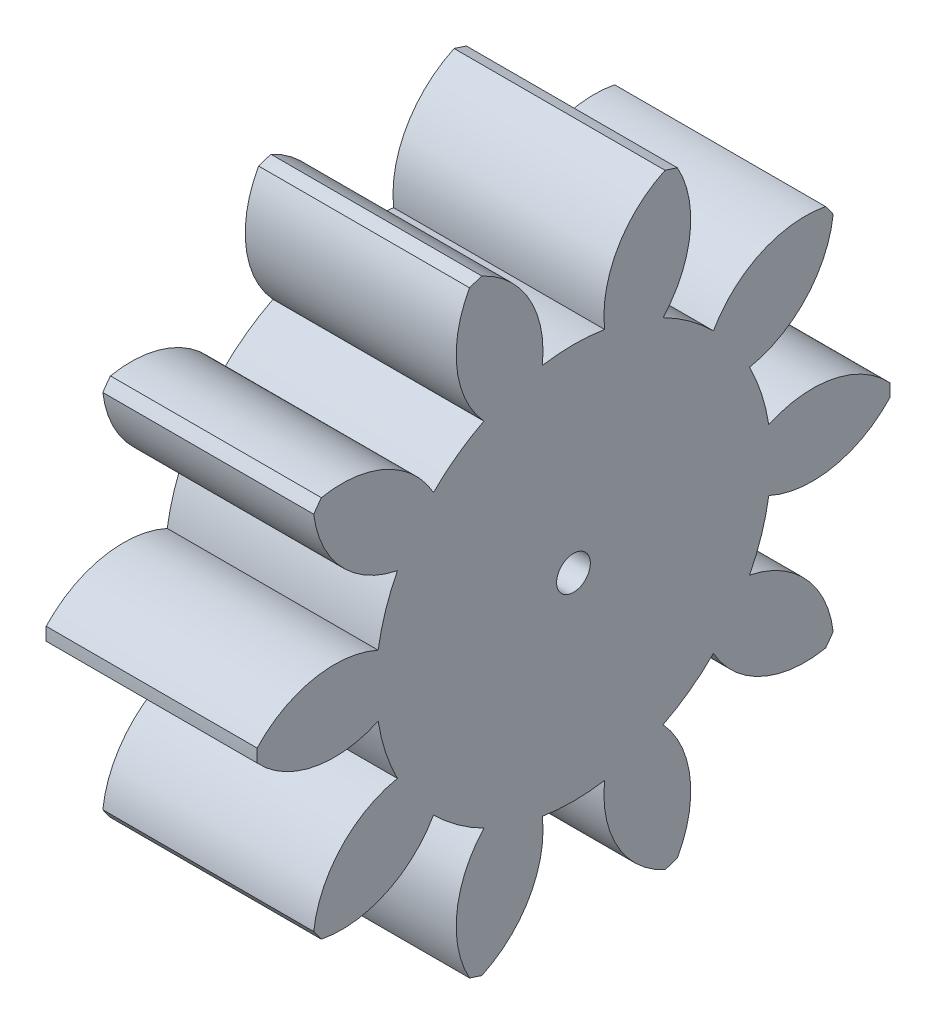
SolidWorks part; units mm, degrees
ref_plane "Plane1" through (0, 0, 0) normal (0, 0, 1) x (1, 0, 0)
ref_plane "Plane2" through (0, 0, 0) normal (0, 1, 0) x (1, 0, 0)
ref_plane "Plane3" through (0, 0, 0) normal (1, 0, 0) x (0, 0, -1)
sketch "HoldingSke" plane through (0, 0, 0) normal (0, 1, 0) x (1, 0, 0)
  line L0 (0, 0) -> (0.7878, -0.1389)
  line L1 (-15, 0) -> (100, 0) construction
  line L2 (0, 0) -> (-2.1039, 2.3779)
  line L3 (0, 0) -> (-11.863, 4.5341)
  line L4 (0, 0) -> (8.5048, 1.4996)
  line L5 (0, 0) -> (-46.8476, -17.4728)
  line L6 (0, 0) -> (-9.9476, -6.7116)
  line L7 (-2.1039, 2.3779) -> (8.6586, 51.2059)
  line L8 (-76.2, 54.61) -> (-76.1, 54.61)
  line L9 (-71.009, 38.7566) -> (-53.1078, 45.2721)
  line L10 (-76.2, 71.12) -> (104.1128, 71.12)
  line L11 (0, 0) -> (-12, 0)
  line L12 (-76.2, 101.6) -> (-76.155, 101.6)
  line L13 (24.9733, 27.94) -> (52.9518, 28.4284)
  line L14 (24.9733, 27.94) -> (24.9743, 27.94)
  line L15 (24.9733, 27.94) -> (100.4006, 29.5858)
  line L16 (-63.627, -1.25) -> (-12.827, -1.25)
  circle A0 centre (0, 0) radius 0.4
  circle A1 centre (0, 0) radius 4.6865
  circle A2 centre (0, 0) radius 37.5
  circle A3 centre (0, 0) radius 0.4
  dimension "MHD" = 9.373
  dimension "Hub_dia" = 75
  dimension "Bore" = 0.8
  dimension "MBD" = 0.8
  dimension "Num_teeth" = 10
  dimension "Pitch" = 0.8
  dimension "Overall_len" = 50
  dimension "Show_teeth" = 10
  dimension "Thickness" = 12
  dimension "OAL" = 50.0001
  dimension "T_dim" = 0.1
  dimension "Ap" = 20
  dimension "H" = 19.05
  dimension "Pitch_radius" = 180.3128
  dimension "Width" = 12
  dimension "Backlash" = 0.045
  dimension "Addendum_fac" = 1
  dimension "Dedendum_fac" = 1.25
  dimension "Clearance_fac" = 0.25
  dimension "Dedendum_add" = 0.001
  dimension "Module" = 1.25
sketch "BasProSke" plane through (0, 0, 0) normal (0, 1, 0) x (1, 0, 0)
  line L0 (-10, 0) -> (60, 0) construction
  line L1 (0, 0) -> (0, 7.5)
  line L2 (0, 0) -> (12, 0)
  line L3 (12, 0) -> (12, 7.5)
  line L4 (12, 7.5) -> (0, 7.5)
  dimension "Thickness" = 12
  dimension "Diameter" = 15
revolve "Base-Revolve" add sketch "BasProSke" angle 360 about L0
sketch "TooCutSke" plane through (0, 0, 0) normal (1, 0, 0) x (0, 0, -1)
  line L1 (0, 0) -> (0, 107) construction
  line L2 (0, 0) -> (-1.0563, 6.1601) construction
  line L3 (0, 0) -> (-3.8225, 11.7646) construction
  line L4 (-1.0563, 6.1601) -> (-1.9113, 5.8823) construction
  arc A0 (0.7377, 4.6281) -> (-0.7377, 4.6281) centre (0, 0) ccw
  arc A1 (2.2058, 7.1949) -> (-2.2058, 7.1949) centre (0, 0) ccw
  circle A2 centre (0, 0) radius 6.25 construction
  circle A3 centre (0, 0) radius 5.8731 construction
  arc A4 (-0.7377, 4.6281) -> (-2.2058, 7.1949) centre (-3.2217, 4.9106) ccw
  arc A5 (2.2058, 7.1949) -> (0.7377, 4.6281) centre (3.2217, 4.9106) ccw
  dimension "Root_dia" = 9.373
  dimension "Overcut_dia" = 15.0508
  dimension "Pitch_dia" = 12.5
  dimension "Base_dia" = 11.7462
  dimension "Flank_rad" = 2.5
  dimension "Half_ang" = 18
  dimension "Half_CT" = 0.899
extrude "ToothCut" cut sketch "TooCutSke" along normal through all
fillet "Breaks" [suppressed] radius 0.025
fillet "RootFillets" [suppressed] radius 0.3135
pattern_circular "TeethCuts" count 10 every 36 about axis through (-10, 0, 0) along (1, 0, 0) of "ToothCut", "RootFillets", "Breaks"
sketch "HubNeaOneSke" plane through (0, 0, 0) normal (-1, 0, 0) x (0, 0, 1)
  circle A0 centre (0, 0) radius 4.6865
  dimension "Diameter" = 9.373
extrude "HubNearOne" [suppressed] add sketch "HubNeaOneSke" along normal blind 38.0001
sketch "HubNeaBotSke" plane through (0, 0, 0) normal (-1, 0, 0) x (0, 0, 1)
  circle A0 centre (0, 0) radius 4.6865
  dimension "Diameter" = 9.373
extrude "HubNearBoth" [suppressed] add sketch "HubNeaBotSke" along normal blind 19
ref_plane "FarPln" through (12, 0, 0) normal (1, 0, 0) x (0, 0, -1)
sketch "HubFarSke" plane through (12, 0, 0) normal (1, 0, 0) x (0, 0, -1)
  circle A0 centre (0, 0) radius 4.6865
  dimension "Diameter" = 9.373
extrude "HubFar" [suppressed] add sketch "HubFarSke" along normal blind 19
sketch "BorSke" plane through (0, 0, 0) normal (1, 0, 0) x (0, 0, -1)
  circle A0 centre (0, 0) radius 0.4
  dimension "Diameter" = 0.8
extrude "Bore" cut sketch "BorSke" along normal mid plane 100.0001
sketch "KeySke" plane through (0, 0, 0) normal (1, 0, 0) x (0, 0, -1)
  line L0 (-0.05, 0) -> (-0.05, 0.5)
  line L1 (-0.05, 0.5) -> (0.05, 0.5)
  line L2 (0.05, 0.5) -> (0.05, 0)
  line L3 (0, 0) -> (0, 34) construction
  line L4 (-0.05, 0) -> (0.05, 0)
  dimension "Offset" = 0.5
  dimension "Width" = 0.1
extrude "Keyway" [suppressed] cut sketch "KeySke" along normal mid plane 100.0001
pattern_circular "Keyway2" [suppressed] count 2 every 90 about axis through (-10, 0, 0) along (1, 0, 0)
sketch "Schizzo1" plane through (12, 0, 0) normal (1, 0, 0) x (0, 0, -1)
  line L1 (-9.3623, 8.3528) -> (9.3623, 8.3528)
  line L2 (-9.3623, 8.3528) -> (-9.3623, -8.3528)
  line L3 (-9.3623, -8.3528) -> (9.3623, -8.3528)
  line L4 (9.3623, 8.3528) -> (9.3623, -8.3528)
  line L5 (-9.3623, 8.3528) -> (9.3623, -8.3528) construction
  line L6 (-9.3623, -8.3528) -> (9.3623, 8.3528) construction
  point P0 (0, 0)
  dimension "D1" = 16.7056
  dimension "D2" = 18.7246
extrude "Taglio-Estrusione1" cut sketch "Schizzo1" against normal blind 7
equation "' \"Module@HoldingSke\" = 6.35"
equation "' \"Num_teeth@HoldingSke\" = 12"
equation "' \"Ap@HoldingSke\" =  20"
equation "' \"Ap@HoldingSke\" = 20"
equation "' \"Width@HoldingSke\" = 0.5 * 25.4"
equation "' \"Hub_dia@HoldingSke\"= 1 * 25.4"
equation "' \"Hub_dia@HoldingSke\" = 1 * 25.4"
equation "' \"Overall_len@HoldingSke\" = 1.0 * 25.4"
equation "' \"Bore@HoldingSke\" = 0.75 * 25.4"
equation "' \"T_dim@HoldingSke\" = 0.1 * 25.4"
equation "' \"Width@KeySke\" = 0.25 * 25.4"
equation "' \"Show_teeth@HoldingSke\" = 13"
equation "' \"Backlash@HoldingSke\" = 0.009 * 25.4"
equation "' \"Addendum_fac@HoldingSke\" = 1.0"
equation "' \"Dedendum_fac@HoldingSke\" = 1.25"
equation "' \"Dedendum_add@HoldingSke\" = 0.00005 * 25.4"
equation "' \"Clearance_fac@HoldingSke\" = 0.25"
equation "\"Pitch@HoldingSke\" = 1 / \"Module@HoldingSke\""
equation "\"Overcut_dia@TooCutSke\" = (\"Num_teeth@HoldingSke\" + 2 * \"Addendum_fac@HoldingSke\") / \"Pitch@HoldingSke\" + 0.002 * 25.4"
equation "\"Pitch_dia@TooCutSke\" = \"Num_teeth@HoldingSke\" / \"Pitch@HoldingSke\""
equation "\"Base_dia@TooCutSke\" = \"Num_teeth@HoldingSke\" / \"Pitch@HoldingSke\" * cos((\"Ap@HoldingSke\"  * 3.14159265 / 180))"
equation "\"Root_dia@TooCutSke\" = (\"Num_teeth@HoldingSke\" + 2) / \"Pitch@HoldingSke\" - 2 * (\"Addendum_fac@HoldingSke\" + \"Dedendum_fac@HoldingSke\") / \"Pitch@HoldingSke\" - \"Dedendum_add@HoldingSke\" * 2"
equation "\"Half_ang@TooCutSke\" = 180 / \"Num_teeth@HoldingSke\""
equation "\"Half_CT@TooCutSke\" = \"Num_teeth@HoldingSke\" / \"Pitch@HoldingSke\" * sin((3.14159265 / 2 / \"Num_teeth@HoldingSke\")) / 2 - 7 * \"Backlash@HoldingSke\" / 4"
equation "\"Flank_rad@TooCutSke\" = \"Num_teeth@HoldingSke\" / \"Pitch@HoldingSke\" / 5"
equation "\"Radius@RootFillets\" = \"Clearance_fac@HoldingSke\" / \"Pitch@HoldingSke\" + \"Dedendum_add@HoldingSke\""
equation "\"Break_rad@Breaks\" = 0.02 / \"Pitch@HoldingSke\""
equation "\"Thickness@HoldingSke\" = \"Width@HoldingSke\""
equation "\"OAL@HoldingSke\" = \"Thickness@HoldingSke\""
equation "\"MHD@HoldingSke\" = (\"Num_teeth@HoldingSke\" + 2) / \"Pitch@HoldingSke\" - 2 * (\"Addendum_fac@HoldingSke\" + \"Dedendum_fac@HoldingSke\")  / \"Pitch@HoldingSke\" - \"Dedendum_add@HoldingSke\" * 2"
equation "\"MBD@HoldingSke\" = (\"Num_teeth@HoldingSke\" + 2) / \"Pitch@HoldingSke\" - 2 * (\"Addendum_fac@HoldingSke\" + \"Dedendum_fac@HoldingSke\")  / \"Pitch@HoldingSke\" - \"Dedendum_add@HoldingSke\" * 2 - 0.002 * 25.4"
equation "\"MHD@HoldingSke\" = ((sgn( \"MHD@HoldingSke\" - \"Hub_dia@HoldingSke\" )-1)*( \"MHD@HoldingSke\" - \"Hub_dia@HoldingSke\" ))/-2+ \"Hub_dia@HoldingSke\""
equation "\"MBD@HoldingSke\" = ((sgn( \"MBD@HoldingSke\" - \"Bore@HoldingSke\" )-1)*( \"MBD@HoldingSke\" - \"Bore@HoldingSke\" ))/-2+ \"Bore@HoldingSke\""
equation "\"OAL@HoldingSke\" = ((sgn( \"OAL@HoldingSke\" - \"Overall_len@HoldingSke\" )+1)*( \"OAL@HoldingSke\" - \"Overall_len@HoldingSke\" ))/2 + \"Overall_len@HoldingSke\" + 0.000002 * 25.4"
equation "\"Num_teeth@TeethCuts\" = int( \"Show_teeth@HoldingSke\" ) + 1"
equation "\"Num_teeth@TeethCuts\" = ((sgn( \"Num_teeth@TeethCuts\" - \"Num_teeth@HoldingSke\" )-1)*( \"Num_teeth@TeethCuts\" - \"Num_teeth@HoldingSke\" ))/-2+ \"Num_teeth@HoldingSke\""
equation "\"Num_teeth@TeethCuts\" = ((sgn( \"Num_teeth@TeethCuts\" - 2.0)+1)*( \"Num_teeth@TeethCuts\" - 2.0))/2 +2.0"
equation "\"Angle@TeethCuts\" = 360.0 / \"Num_teeth@HoldingSke\""
equation "\"Diameter@BasProSke\" = (\"Num_teeth@HoldingSke\" + 2 * \"Addendum_fac@HoldingSke\") / \"Pitch@HoldingSke\""
equation "\"Thickness@BasProSke\"  = \"Thickness@HoldingSke\""
equation "' \"Fillet_rad@BasProSke\" =  \"Thickness@HoldingSke\" * 0.05"
equation "' \"Fillet_rad@BasProSke\" = \"Thickness@HoldingSke\" * 0.05"
equation "\"MHD@HoldingSke\" = ((sgn( \"MHD@HoldingSke\" - \"Root_dia@TooCutSke\" )-1)*( \"MHD@HoldingSke\" - \"Root_dia@TooCutSke\" ))/-2+ \"Root_dia@TooCutSke\""
equation "\"Diameter@HubNeaOneSke\" = \"MHD@HoldingSke\""
equation "\"Length@HubNearOne\" = \"OAL@HoldingSke\" - \"Thickness@BasProSke\""
equation "\"Diameter@HubNeaBotSke\" = \"MHD@HoldingSke\""
equation "\"Length@HubNearBoth\" = ( \"OAL@HoldingSke\" - \"Thickness@BasProSke\" ) / 2.0"
equation "\"Thickness@FarPln\" = \"Thickness@BasProSke\""
equation "\"Diameter@HubFarSke\" = \"MHD@HoldingSke\""
equation "\"Length@HubFar\" = ( \"OAL@HoldingSke\" - \"Thickness@BasProSke\" ) / 2.0"
equation "\"Diameter@BorSke\" = \"MBD@HoldingSke\""
equation "\"D1@Bore\" = \"OAL@HoldingSke\" * 2.0"
equation "\"D1@Keyway\" = \"OAL@HoldingSke\" * 2.0"
equation "\"Offset@KeySke\" = \"T_dim@HoldingSke\" + \"MBD@HoldingSke\" / 2.0"
